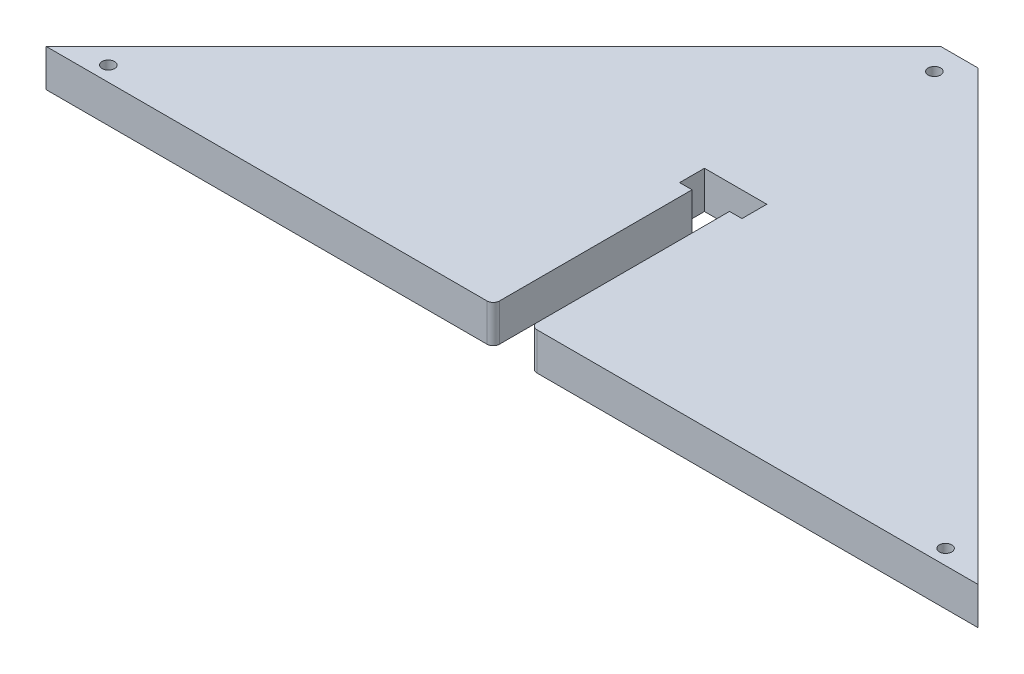
SolidWorks part; units mm, degrees
ref_plane "Front Plane" through (0, 0, 0) normal (0, 0, 1) x (1, 0, 0)
ref_plane "Top Plane" through (0, 0, 0) normal (0, 1, 0) x (1, 0, 0)
ref_plane "Right Plane" through (0, 0, 0) normal (1, 0, 0) x (0, 0, -1)
sketch "Sketch2" plane through (0, 0, 0) normal (0, 1, 0) x (1, 0, 0)
  line L0 (-191.3973, -33.4506) -> (21.5527, -33.4506)
  line L1 (81.1027, 239.0494) -> (58.6027, 216.5494) construction
  line L2 (42.6527, 182.4994) -> (258.6027, -33.4506)
  line L3 (-191.3973, -33.4506) -> (24.5527, 182.4994)
  line L4 (33.6027, 259.9994) -> (33.6027, -12.5006) construction
  line L5 (42.6527, 74.5244) -> (48.6527, 74.5244)
  line L6 (-13.8973, 239.0494) -> (8.6027, 216.5494) construction
  line L7 (24.5527, 182.4994) -> (42.6527, 182.4994)
  line L8 (24.5527, 74.5244) -> (42.6527, 74.5244)
  line L9 (48.6527, 74.5244) -> (48.6527, 62.5244)
  line L10 (42.6527, 62.5244) -> (42.6527, -30.4506)
  line L11 (48.6527, 62.5244) -> (42.6527, 62.5244)
  line L12 (18.5527, 62.5244) -> (18.5527, 74.5244)
  line L13 (18.5527, 74.5244) -> (24.5527, 74.5244)
  line L14 (24.5527, 62.5244) -> (18.5527, 62.5244)
  line L15 (150.6277, 191.5494) -> (-83.4223, 191.5494) construction
  line L16 (258.6027, -33.4506) -> (-83.4223, 74.5244) construction
  line L17 (24.5527, 182.4994) -> (24.5527, 128.3956) construction
  line L18 (24.5527, 62.5244) -> (24.5527, -30.4506)
  line L19 (45.6527, -33.4506) -> (258.6027, -33.4506)
  line L20 (42.6527, 182.4994) -> (42.6527, 128.3956) construction
  line L21 (-191.3973, -33.4506) -> (150.6277, 74.5244) construction
  arc A0 (42.6527, -30.4506) -> (45.6527, -33.4506) centre (45.6527, -30.4506) ccw
  arc A1 (21.5527, -33.4506) -> (24.5527, -30.4506) centre (21.5527, -30.4506) ccw
  circle A2 centre (33.6027, 170.4994) radius 3
  circle A3 centre (235.716, -26.2254) radius 3
  circle A4 centre (-168.5107, -26.2254) radius 3
  point P2 (13.6027, 8.5494)
  point P4 (88.6027, 244.0494)
  point P5 (33.6027, -33.4506)
  point P6 (203.6027, 246.5494)
  point P7 (33.6027, 191.5494)
  point P11 (14.6027, 11.5494)
  point P12 (42.6527, -33.4506)
  point P13 (-31.3973, 184.0494)
  point P14 (13.6027, 14.5494)
  point P15 (13.6027, 12.5494)
  point P16 (-33.3973, 12.5494)
  point P17 (-31.3973, 199.0494)
  point P39 (33.6027, 191.5494)
  dimension "D9" = 6
  dimension "D10" = 6
  dimension "D13" = 6
  dimension "D15" = 6
  dimension "D18" = 6
  dimension "D3" = 450
  dimension "D5" = 215.95
  dimension "D6" = 225
  dimension "D4" = 18.1
  dimension "D7" = 107.975
  dimension "D17" = 9.05
  dimension "D2" = 9.05
  dimension "D8" = 12
  dimension "D11" = 6
  dimension "D12" = 6
  dimension "D14" = 12
  dimension "D16" = 24
  dimension "D19" = 24
extrude "Boss-Extrude1" add sketch "Sketch2" along normal blind 18.1
equation "\"D5@Sketch2\"=\"D3@Sketch2\"/2-(\"D4@Sketch2\"/2)"
equation "\"D6@Sketch2\"=\"D3@Sketch2\"/2"
equation "\"D10@Sketch2\"=\"D9@Sketch2\""
equation "\"D7@Sketch2\"=\"D3@Sketch2\"/4-(\"D17@Sketch2\"/2)"
equation "\"D17@Sketch2\"=\"D4@Sketch2\"/2"
equation "\"D2@Sketch2\"=\"D4@Sketch2\"/2"
equation "\"spessore\"= 18.1mm"
equation "\"larghezza\"= 450mm"
equation "\"punta_fresa\"= 6mm"
equation "\"D3@Sketch2\"=\"larghezza\""
equation "\"D4@Sketch2\"=\"spessore\""
equation "\"D9@Sketch2\"=\"punta_fresa\""
equation "\"D8@Sketch2\"=\"punta_fresa\"*2"
equation "\"D11@Sketch2\"=\"punta_fresa\""
equation "\"D12@Sketch2\"=\"punta_fresa\""
equation "\"D13@Sketch2\"=\"punta_fresa\""
equation "\"D14@Sketch2\"=\"punta_fresa\"*2"
equation "\"D15@Sketch2\"=\"punta_fresa\""
equation "\"D16@Sketch2\"=\"punta_fresa\"*4"
equation "\"D18@Sketch2\"=\"punta_fresa\""
equation "\"D19@Sketch2\"=\"punta_fresa\"*4"
equation "\"D1@Boss-Extrude1\"=\"spessore\""
